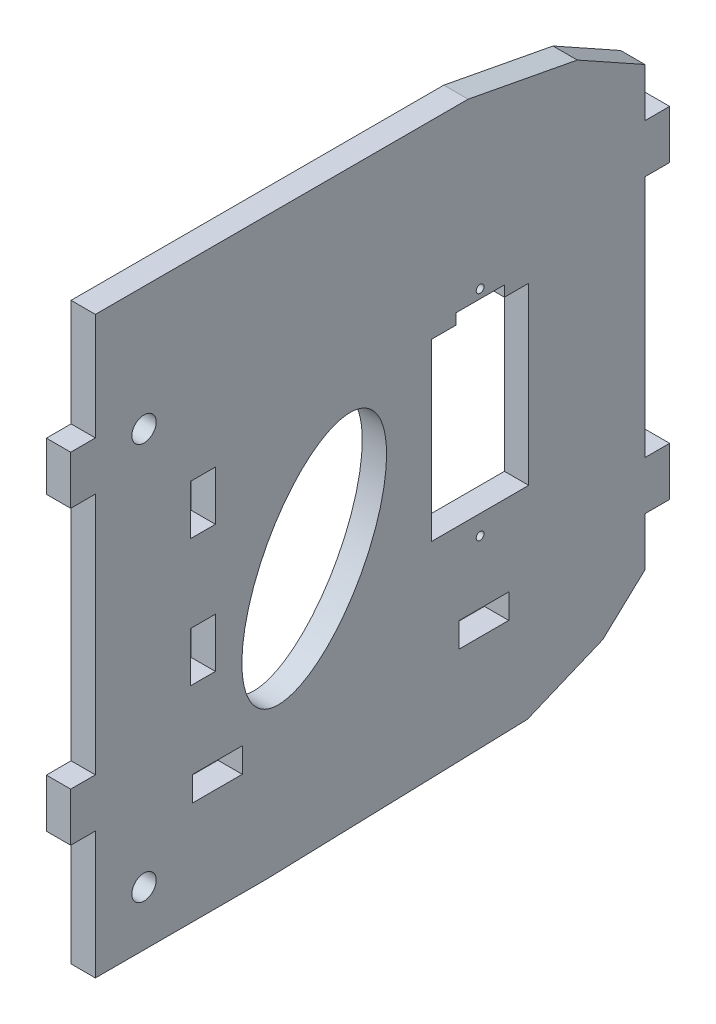
SolidWorks part; units mm, degrees
ref_plane "Front Plane" through (0, 0, 0) normal (0, 0, 1) x (1, 0, 0)
ref_plane "Top Plane" through (0, 0, 0) normal (0, 1, 0) x (1, 0, 0)
ref_plane "Right Plane" through (0, 0, 0) normal (1, 0, 0) x (0, 0, -1)
sketch "Sketch1" plane through (0, 0, 0) normal (1, 0, 0) x (0, 0, -1)
  line L1 (35.8775, -28.575) -> (-35.8775, -28.575)
  line L2 (35.8775, -28.575) -> (35.8775, 28.575)
  line L3 (35.8775, 28.575) -> (-35.8775, 28.575)
  line L4 (-35.8775, -28.575) -> (-35.8775, 28.575)
  line L5 (35.8775, -28.575) -> (-35.8775, 28.575) construction
  line L6 (35.8775, 28.575) -> (-35.8775, -28.575) construction
  point P0 (0, 0)
  dimension "D1" = 57.15
  dimension "D2" = 71.755
extrude "main body" add sketch "Sketch1" along normal blind 3.175
sketch "Sketch2" plane through (0, 0, 0) normal (-1, 0, 0) x (0, 0, 1)
  line L0 (35.8775, 22.225) -> (39.1033, 22.225)
  line L1 (35.8775, 28.575) -> (35.8775, -28.575) construction
  line L2 (39.1033, 22.225) -> (39.1033, 15.875)
  line L3 (39.1033, 15.875) -> (35.8775, 15.875)
  line L4 (35.8775, 15.875) -> (35.8775, 22.225)
  line L5 (35.8775, -15.875) -> (39.1033, -15.875)
  line L6 (39.1033, -15.875) -> (39.1033, -22.225)
  line L7 (39.1033, -22.225) -> (35.8775, -22.225)
  line L8 (35.8775, -22.225) -> (35.8775, -15.875)
  line L9 (-35.8775, 28.575) -> (35.8775, 28.575) construction
  line L10 (35.8775, -28.575) -> (-35.8775, -28.575) construction
  dimension "D1" = 6.35
  dimension "D2" = 3.2258
  dimension "D3" = 3.2258
  dimension "D4" = 6.35
  dimension "D5" = 31.75
  dimension "D6" = 6.35
  dimension "D7" = 6.35
extrude "tabs front" add sketch "Sketch2" against normal blind 3.175
mirror "mirror of tabs (back)" about plane through (0, 0, 0) normal (0, 0, 1) of "tabs front"
sketch "Sketch3" plane through (0, 0, 0) normal (-1, 0, 0) x (0, 0, 1)
  line L0 (35.8775, 15.875) -> (35.8775, -15.875) construction
  line B0 (-20.7062, -11.43) -> (-8.0062, -11.43)
  line B1 (-20.7062, -11.43) -> (-20.7062, 11.43)
  line B2 (-20.7062, 11.43) -> (-17.5312, 11.43)
  line B3 (-8.0062, -11.43) -> (-8.0062, 11.43)
  line B4 (-17.5312, 11.43) -> (-17.5312, 12.827)
  line B5 (-17.5312, 12.827) -> (-11.1812, 12.827)
  line B6 (-11.1812, 11.43) -> (-11.1812, 12.827)
  line B7 (-11.1812, 11.43) -> (-8.0062, 11.43)
  circle B8 centre (-14.3562, 13.97) radius 0.508
  circle B9 centre (-14.3562, -13.97) radius 0.508
  dimension "D1" = 50.2337
  dimension "D2" = 23.241
sketch_block_instance "servo_hole_SG90-1"
sketch_block "servo_hole_SG90" parameters "D5"=1.016, "D6"=1.016, "D9"=2.1092, "D1"=27.94, "D2"=6.35, "D3"=22.86, "D4"=12.7, "D7"=1.397, "D8"=6.35
extrude "cut for ear motor" cut sketch "Sketch3" against normal through all
sketch "Sketch4" plane through (0, 0, 0) normal (-1, 0, 0) x (0, 0, 1)
  line L0 (35.8775, 15.875) -> (35.8775, -15.875) construction
  line L1 (20.2057, 11.0998) -> (23.4315, 11.0998)
  line L2 (20.2057, 11.0998) -> (20.2057, 4.6228)
  line L3 (20.2057, 4.6228) -> (23.4315, 4.6228)
  line L4 (23.4315, 11.0998) -> (23.4315, 4.6228)
  line L5 (20.2057, 11.0998) -> (23.4315, 4.6228) construction
  line L6 (20.2057, 4.6228) -> (23.4315, 11.0998) construction
  line L7 (20.2057, -5.5372) -> (23.4315, -5.5372)
  line L8 (20.2057, -5.5372) -> (20.2057, -12.0142)
  line L9 (20.2057, -12.0142) -> (23.4315, -12.0142)
  line L10 (23.4315, -5.5372) -> (23.4315, -12.0142)
  line L11 (20.2057, -5.5372) -> (23.4315, -12.0142) construction
  line L12 (20.2057, -12.0142) -> (23.4315, -5.5372) construction
  line L14 (35.8775, -28.575) -> (-35.8775, -28.575) construction
  line L15 (16.7005, -25.4) -> (23.1775, -25.4)
  line L16 (16.7005, -25.4) -> (16.7005, -22.1742)
  line L17 (16.7005, -22.1742) -> (23.1775, -22.1742)
  line L18 (23.1775, -25.4) -> (23.1775, -22.1742)
  line L19 (16.7005, -25.4) -> (23.1775, -22.1742) construction
  line L20 (16.7005, -22.1742) -> (23.1775, -25.4) construction
  line L21 (-18.0975, -25.4) -> (-11.6205, -25.4)
  line L22 (-18.0975, -25.4) -> (-18.0975, -22.1742)
  line L23 (-18.0975, -22.1742) -> (-11.6205, -22.1742)
  line L24 (-11.6205, -25.4) -> (-11.6205, -22.1742)
  line L25 (-18.0975, -25.4) -> (-11.6205, -22.1742) construction
  line L26 (-18.0975, -22.1742) -> (-11.6205, -25.4) construction
  line L28 (35.8775, -22.225) -> (35.8775, -28.575) construction
  point P0 (21.8186, 7.8613)
  point P5 (21.8186, -8.7757)
  point P14 (19.939, -23.7871)
  point P19 (-14.859, -23.7871)
  dimension "D1" = 6.477
  dimension "D2" = 3.2258
  dimension "D3" = 3.2258
  dimension "D4" = 6.477
  dimension "D5" = 12.446
  dimension "D6" = 12.446
  dimension "D7" = 10.16
  dimension "D8" = 10.16
  dimension "D9" = 3.175
  dimension "D10" = 3.175
  dimension "D11" = 6.477
  dimension "D12" = 6.477
  dimension "D13" = 28.321
  dimension "D14" = 12.7
  dimension "D15" = 3.2258
  dimension "D16" = 3.2258
extrude "cut for tabs" cut sketch "Sketch4" against normal through all
sketch "Sketch5" plane through (0, 0, 0) normal (-1, 0, 0) x (0, 0, 1)
  line L0 (-35.8775, -28.575) -> (35.8775, -28.575)
  line L1 (-12.7873, 36.195) -> (-27.0464, 33.4924)
  line L2 (13.5233, -38.8467) -> (-20.5286, -37.8018)
  line L3 (-20.5286, -37.8018) -> (-30.3633, -33.7109)
  line L4 (-30.3633, -33.7109) -> (-35.8775, -28.575)
  line L5 (35.8775, -28.575) -> (35.8775, -38.8467)
  line L6 (35.8775, 28.575) -> (35.8775, 36.195)
  line L7 (-12.7873, 36.195) -> (26.2002, 36.195)
  line L8 (-27.0464, 33.4924) -> (-35.8775, 28.575)
  line L10 (35.8775, 36.195) -> (26.2002, 36.195)
  line L11 (-35.8775, 28.575) -> (35.8775, 28.575)
  line L12 (35.8775, -38.8467) -> (13.5233, -38.8467)
extrude "Boss-Extrude1" add sketch "Sketch5" against normal blind 3.175
sketch "Sketch6" plane through (0, 0, 0) normal (-1, 0, 0) x (0, 0, 1)
  line L0 (35.8775, 36.195) -> (-12.7873, 36.195) construction
  line L1 (35.8775, 36.195) -> (35.8775, 22.225) construction
  line L2 (35.8775, -22.225) -> (35.8775, -38.8467) construction
  line L3 (13.5233, -38.8467) -> (35.8775, -38.8467) construction
  circle A0 centre (29.5275, 20.066) radius 1.5875
  circle A1 centre (29.5275, -31.7347) radius 1.5875
  dimension "D1" = 3.175
  dimension "D4" = 3.175
  dimension "D2" = 16.129
  dimension "D3" = 6.35
  dimension "D5" = 6.35
  dimension "D6" = 7.112
extrude "cut for face plate mount screw" cut sketch "Sketch6" against normal through all
sketch "Sketch7" plane through (0, 0, 0) normal (-1, 0, 0) x (0, 0, 1)
  line L0 (0.8618, 8.0971) -> (13.7432, -19.5271) construction
  line L1 (35.8775, 15.875) -> (35.8775, -15.875) construction
  line L2 (35.8775, -4.4122) -> (-35.8775, -4.4122) construction
  line L3 (-35.8775, -15.875) -> (-35.8775, 15.875) construction
  line L4 (35.8775, 36.195) -> (-12.7873, 36.195) construction
  ellipse E0 centre (7.3025, -5.715) end of major axis (13.7432, -19.5271) minor radius 7.62
  dimension "D1" = 7.62
  dimension "D2" = 15.24
  dimension "D3" = 65
  dimension "D4" = 28.575
  dimension "D5" = 41.91
extrude "ellipse cut" cut sketch "Sketch7" against normal through all
